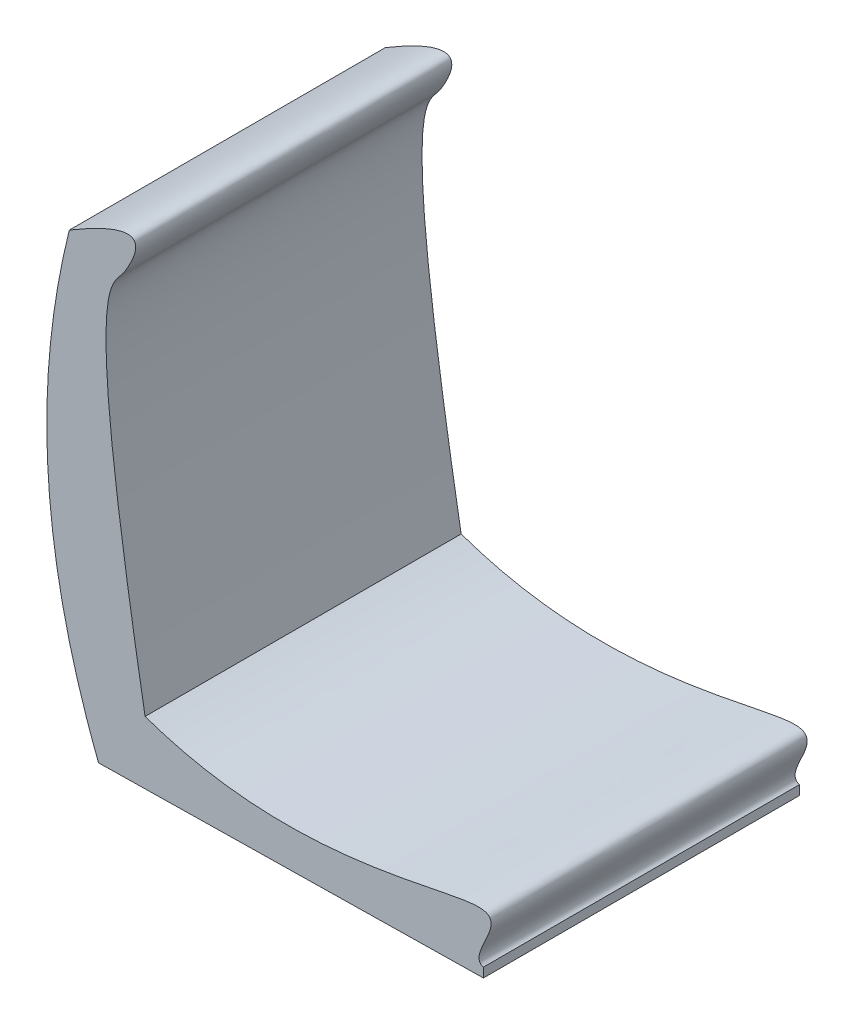
SolidWorks part; units mm, degrees
ref_plane "Front Plane" through (0, 0, 0) normal (0, 0, 1) x (1, 0, 0)
ref_plane "Top Plane" through (0, 0, 0) normal (0, 1, 0) x (1, 0, 0)
ref_plane "Right Plane" through (0, 0, 0) normal (1, 0, 0) x (0, 0, -1)
sketch "Sketch1" plane through (0, 0, 0) normal (0, 0, 1) x (1, 0, 0)
  line L0 (-81.2305, 4.2813) -> (363.7695, 11.3362) construction
  line L1 (-43.242, 4.8836) -> (363.7695, 11.3362)
  line L2 (-50.0916, -5.2263) -> (363.928, 1.3375)
  line L3 (-81.5169, 475.3674) -> (-71.8148, 472.9444)
  line L4 (363.7695, 11.3362) -> (363.928, 1.3375)
  spline S0 degree 2 poles (-71.8148, 472.9444) (-131.107, 235.523) (-43.242, 4.8836) knots 0 0 0 1 1 1
  spline S1 degree 1 poles (-81.5169, 475.3674) (-50.0916, -5.2263) knots 0 0 1 1 construction
  spline S2 degree 3 poles (-81.5169, 475.3674) (-82.7811, 470.3049) (-85.2215, 460.1382) (-89.6924, 439.867) (-94.5385, 414.5395) (-99.1563, 384.1993) (-103.7184, 343.8062) (-106.4274, 293.4377) (-104.885, 233.2046) (-98.5488, 173.196) (-89.2772, 123.389) (-79.4671, 83.6677) (-70.9173, 53.946) (-62.7892, 29.2169) (-56.5943, 11.9661) (-52.8797, 2.0692) (-51.021, -2.7868) (-50.0916, -5.2263) knots 0 0 0 0 0.031694 0.063387 0.126775 0.190162 0.25355 0.380325 0.5071 0.633875 0.760649 0.824037 0.887424 0.950812 0.982506 0.998352 1.014199 1.014199 1.014199 1.014199
  dimension "D1" = 10
  dimension "D3" = 445
extrude "Boss-Extrude1" add sketch "Sketch1" along normal mid plane 340
sketch "Sketch3" plane through (0, 0, -170) normal (0, 0, -1) x (-1, 0, 0)
  line L1 (-363.7695, 11.3362) -> (50.1298, 4.6143)
  spline S0 degree 3 poles (-363.7695, 11.3362) (-344.8762, 18.2393) (-451.4419, 117.7757) (-163.678, 5.3792) (0, 63.0194) knots 0 0 0 0 0.394178 0.872405 0.872405 0.872405 0.872405
  spline S1 degree 2 poles (50.1298, 4.6143) (131.4862, 236.0498) (81.5169, 475.3674) knots 0 0 0 1 1 1
  spline S2 degree 3 poles (81.5169, 475.3674) (-9.8142, 530.1273) (16.9494, 472.9682) (35.7109, 447.2922) (64.2805, 428.6783) (0, 63.0194) knots 0 0 0 0 0.24332 0.34332 1 1 1 1
extrude "Boss-Extrude5" add sketch "Sketch3" against normal up to surface (340 mm away) up to face at (79.9343, 161.1515, 170)
